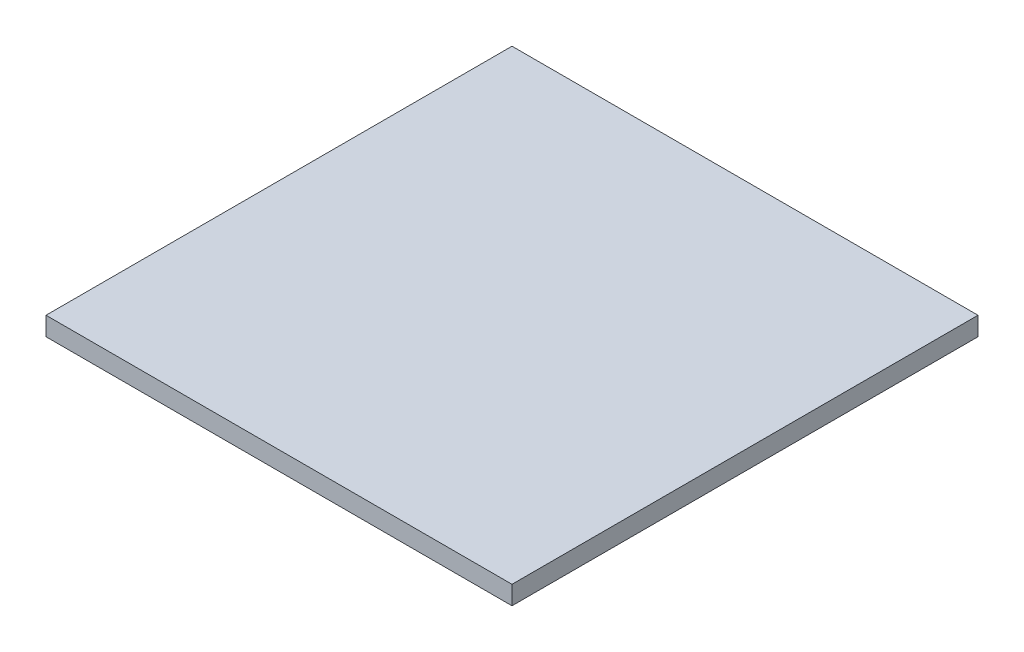
SolidWorks part; units mm, degrees
ref_plane "Front Plane" through (0, 0, 0) normal (0, 0, 1) x (1, 0, 0)
ref_plane "Top Plane" through (0, 0, 0) normal (0, 1, 0) x (1, 0, 0)
ref_plane "Right Plane" through (0, 0, 0) normal (1, 0, 0) x (0, 0, -1)
sketch "Sketch1" plane through (0, 0, 0) normal (0, 1, 0) x (1, 0, 0)
  line L1 (-150, 150) -> (150, 150)
  line L2 (-150, 150) -> (-150, -150)
  line L3 (-150, -150) -> (150, -150)
  line L4 (150, 150) -> (150, -150)
  line L5 (-150, 150) -> (150, -150) construction
  line L6 (-150, -150) -> (150, 150) construction
  point P0 (0, 0)
  dimension "D1" = 300
extrude "Boss-Extrude1" add sketch "Sketch1" along normal blind 12
